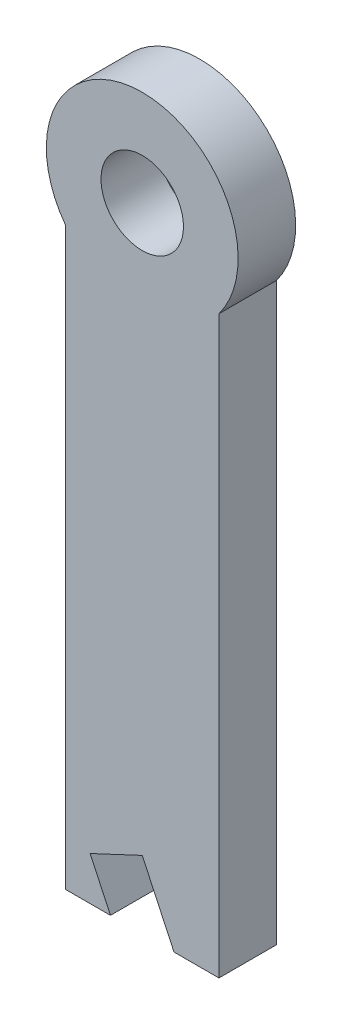
SolidWorks part; units mm, degrees
ref_plane "Front Plane" through (0, 0, 0) normal (0, 0, 1) x (1, 0, 0)
ref_plane "Top Plane" through (0, 0, 0) normal (0, 1, 0) x (1, 0, 0)
ref_plane "Right Plane" through (0, 0, 0) normal (1, 0, 0) x (0, 0, -1)
sketch "Sketch1" plane through (0, 0, 0) normal (0, 0, 1) x (1, 0, 0)
  line L0 (0, 7.2541) -> (0, -37.5953) construction
  line L1 (4, -3) -> (4, -33)
  line L2 (4, -33) -> (1.6564, -33)
  line L3 (-4, -33) -> (-1.6564, -33)
  line L4 (-4, -3) -> (-4, -33)
  line L5 (1.6564, -33) -> (0, -29.4636)
  line L6 (0, -29.4636) -> (-2.7168, -30.736)
  line L7 (-1.6564, -33) -> (-2.7168, -30.736)
  circle A0 centre (0, 0) radius 2.15
  circle A1 centre (0, 0) radius 5
  dimension "D1" = 4.3
  dimension "D2" = 10
  dimension "D3" = 30
  dimension "D4" = 4
  dimension "D5" = 3
  dimension "D6" = 2.5
extrude "Boss-Extrude1" add sketch "Sketch1" along normal blind 3 contours A1 L0 L5 L2 L1 | L0 A1 L4 L3 L7 L6 | L0 A1 A0 | A1 L0 A0
